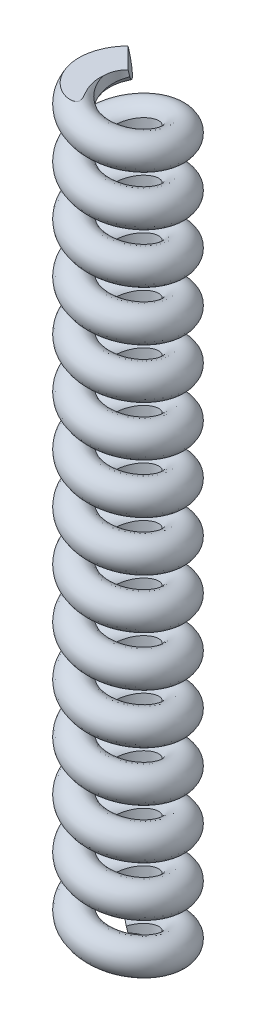
SolidWorks part; units mm, degrees
ref_plane "Front" through (0, 0, 0) normal (0, 0, 1) x (1, 0, 0)
ref_plane "Top" through (0, 0, 0) normal (0, 1, 0) x (1, 0, 0)
ref_plane "Right" through (0, 0, 0) normal (1, 0, 0) x (0, 0, -1)
sketch "Sketch1" plane through (0, 0, 0) normal (0, 1, 0) x (1, 0, 0)
  circle A0 centre (0, 0) radius 3.175
  point P4 (0, 0)
  dimension "D1" = 6.35
curve "Helix/Spiral1" pitch 4.155 height 62.3249 turns 15
sweep "Sweep1" add path "Helix/Spiral1" circular profile diameter 2.54 parameters "D3"=2.54
sketch "Sketch10" plane through (0, 0, 0) normal (1, 0, 0) x (0, 0, -1)
  line L5 (-10.2566, 86.0926) -> (14.7467, 86.0926)
  line L6 (-10.2566, 86.0926) -> (-10.2566, 62.3249)
  line L7 (-10.2566, 62.3249) -> (14.7467, 62.3249)
  line L8 (14.7467, 86.0926) -> (14.7467, 62.3249)
  line L9 (-7.3012, 0) -> (8.8113, 0)
  line L10 (-7.3012, 0) -> (-7.3012, -4.697)
  line L11 (-7.3012, -4.697) -> (8.8113, -4.697)
  line L12 (8.8113, 0) -> (8.8113, -4.697)
  spline S0 degree 3 poles (2.2451, 0) (2.5371, 0.086) (3.0105, 0.2599) (3.2574, 0.5193) (3.0097, 0.7791) (2.3035, 1.0387) (1.2467, 1.2984) (0, 1.5581) (-1.2467, 1.8178) (-2.3035, 2.0775) (-3.0097, 2.3372) (-3.2577, 2.5969) (-3.0097, 2.8566) (-2.3035, 3.1162) (-0.8944, 3.4625) (0.8944, 3.8087) (2.3035, 4.155) (3.0097, 4.4147) (3.2577, 4.6744) (3.0097, 4.9341) (2.3035, 5.1937) (0.8944, 5.54) (-0.8944, 5.8862) (-2.3035, 6.2325) (-3.0097, 6.4922) (-3.2577, 6.7519) (-3.0097, 7.0115) (-2.3035, 7.2712) (-0.8944, 7.6175) (0.8944, 7.9637) (2.3035, 8.31) (3.0097, 8.5697) (3.2577, 8.8294) (3.0097, 9.089) (2.3035, 9.3487) (0.8944, 9.695) (-0.8944, 10.0412) (-2.3035, 10.3875) (-3.0097, 10.6472) (-3.2577, 10.9069) (-3.0097, 11.1665) (-2.3035, 11.4262) (-0.8944, 11.7725) (0.8944, 12.1187) (2.3035, 12.465) (3.0097, 12.7247) (3.2577, 12.9843) (3.0097, 13.244) (2.3035, 13.5037) (0.8944, 13.85) (-0.8944, 14.1962) (-2.3035, 14.5425) (-3.0097, 14.8022) (-3.2577, 15.0618) (-3.0097, 15.3215) (-2.3035, 15.5812) (-0.8944, 15.9275) (0.8944, 16.2737) (2.3035, 16.62) (3.0097, 16.8797) (3.2577, 17.1393) (3.0097, 17.399) (2.3035, 17.6587) (0.8944, 18.005) (-0.8944, 18.3512) (-2.3035, 18.6975) (-3.0097, 18.9572) (-3.2577, 19.2168) (-3.0097, 19.4765) (-2.3035, 19.7362) (-0.8944, 20.0825) (0.8944, 20.4287) (2.3035, 20.775) (3.0097, 21.0346) (3.2577, 21.2943) (3.0097, 21.554) (2.3035, 21.8137) (0.8944, 22.16) (-0.8944, 22.5062) (-2.3035, 22.8525) (-3.0097, 23.1121) (-3.2577, 23.3718) (-3.0097, 23.6315) (-2.3035, 23.8912) (-0.8944, 24.2375) (0.8944, 24.5837) (2.3035, 24.93) (3.0097, 25.1896) (3.2577, 25.4493) (3.0097, 25.709) (2.3035, 25.9687) (0.8944, 26.3149) (-0.8944, 26.6612) (-2.3035, 27.0074) (-3.0097, 27.2671) (-3.2577, 27.5268) (-3.0097, 27.7865) (-2.3035, 28.0462) (-0.8944, 28.3924) (0.8944, 28.7387) (2.3035, 29.0849) (3.0097, 29.3446) (3.2577, 29.6043) (3.0097, 29.864) (2.3035, 30.1237) (0.8944, 30.4699) (-0.8944, 30.8162) (-2.3035, 31.1624) (-3.0097, 31.4221) (-3.2577, 31.6818) (-3.0097, 31.9415) (-2.3035, 32.2012) (-0.8944, 32.5474) (0.8944, 32.8937) (2.3035, 33.2399) (3.0097, 33.4996) (3.2577, 33.7593) (3.0097, 34.019) (2.3035, 34.2787) (0.8944, 34.6249) (-0.8944, 34.9712) (-2.3035, 35.3174) (-3.0097, 35.5771) (-3.2577, 35.8368) (-3.0097, 36.0965) (-2.3035, 36.3562) (-0.8944, 36.7024) (0.8944, 37.0487) (2.3035, 37.3949) (3.0097, 37.6546) (3.2577, 37.9143) (3.0097, 38.174) (2.3035, 38.4337) (0.8944, 38.7799) (-0.8944, 39.1262) (-2.3035, 39.4724) (-3.0097, 39.7321) (-3.2577, 39.9918) (-3.0097, 40.2515) (-2.3035, 40.5112) (-0.8944, 40.8574) (0.8944, 41.2037) (2.3035, 41.5499) (3.0097, 41.8096) (3.2577, 42.0693) (3.0097, 42.329) (2.3035, 42.5887) (0.8944, 42.9349) (-0.8944, 43.2812) (-2.3035, 43.6274) (-3.0097, 43.8871) (-3.2577, 44.1468) (-3.0097, 44.4065) (-2.3035, 44.6662) (-0.8944, 45.0124) (0.8944, 45.3587) (2.3035, 45.7049) (3.0097, 45.9646) (3.2577, 46.2243) (3.0097, 46.484) (2.3035, 46.7437) (0.8944, 47.0899) (-0.8944, 47.4362) (-2.3035, 47.7824) (-3.0097, 48.0421) (-3.2577, 48.3018) (-3.0097, 48.5615) (-2.3035, 48.8212) (-0.8944, 49.1674) (0.8944, 49.5137) (2.3035, 49.8599) (3.0097, 50.1196) (3.2577, 50.3793) (3.0097, 50.639) (2.3035, 50.8987) (0.8944, 51.2449) (-0.8944, 51.5912) (-2.3035, 51.9374) (-3.0097, 52.1971) (-3.2577, 52.4568) (-3.0097, 52.7165) (-2.3035, 52.9761) (-0.8944, 53.3224) (0.8944, 53.6686) (2.3035, 54.0149) (3.0097, 54.2746) (3.2577, 54.5343) (3.0097, 54.794) (2.3035, 55.0536) (0.8944, 55.3999) (-0.8944, 55.7461) (-2.3035, 56.0924) (-3.0097, 56.3521) (-3.2577, 56.6118) (-3.0097, 56.8715) (-2.3035, 57.1311) (-0.8944, 57.4774) (0.8944, 57.8236) (2.3035, 58.1699) (3.0097, 58.4296) (3.2577, 58.6893) (3.0097, 58.9489) (2.3035, 59.2086) (0.8944, 59.5549) (-0.8944, 59.9011) (-2.3035, 60.2474) (-3.0097, 60.5071) (-3.2577, 60.7668) (-3.0097, 61.0264) (-2.3035, 61.2861) (-1.2467, 61.5458) (0.0002, 61.8056) (1.2458, 62.0649) (1.953, 62.2388) (2.2451, 62.3249) knots 0 0 0 0 0.004167 0.008333 0.0125 0.016667 0.020833 0.025 0.029167 0.033333 0.0375 0.041667 0.045833 0.05 0.054167 0.0625 0.066667 0.070833 0.075 0.079167 0.083333 0.0875 0.095833 0.1 0.104167 0.108333 0.1125 0.116667 0.120833 0.129167 0.133333 0.1375 0.141667 0.145833 0.15 0.154167 0.1625 0.166667 0.170833 0.175 0.179167 0.183333 0.1875 0.195833 0.2 0.204167 0.208333 0.2125 0.216667 0.220833 0.229167 0.233333 0.2375 0.241667 0.245833 0.25 0.254167 0.2625 0.266667 0.270833 0.275 0.279167 0.283333 0.2875 0.295833 0.3 0.304167 0.308333 0.3125 0.316667 0.320833 0.329167 0.333333 0.3375 0.341667 0.345833 0.35 0.354167 0.3625 0.366667 0.370833 0.375 0.379167 0.383333 0.3875 0.395833 0.4 0.404167 0.408333 0.4125 0.416667 0.420833 0.429167 0.433333 0.4375 0.441667 0.445833 0.45 0.454167 0.4625 0.466667 0.470833 0.475 0.479167 0.483333 0.4875 0.495833 0.5 0.504167 0.508333 0.5125 0.516667 0.520833 0.529167 0.533333 0.5375 0.541667 0.545833 0.55 0.554167 0.5625 0.566667 0.570833 0.575 0.579167 0.583333 0.5875 0.595833 0.6 0.604167 0.608333 0.6125 0.616667 0.620833 0.629167 0.633333 0.6375 0.641667 0.645833 0.65 0.654167 0.6625 0.666667 0.670833 0.675 0.679167 0.683333 0.6875 0.695833 0.7 0.704167 0.708333 0.7125 0.716667 0.720833 0.729167 0.733333 0.7375 0.741667 0.745833 0.75 0.754167 0.7625 0.766667 0.770833 0.775 0.779167 0.783333 0.7875 0.795833 0.8 0.804167 0.808333 0.8125 0.816667 0.820833 0.829167 0.833333 0.8375 0.841667 0.845833 0.85 0.854167 0.8625 0.866667 0.870833 0.875 0.879167 0.883333 0.8875 0.895833 0.9 0.904167 0.908333 0.9125 0.916667 0.920833 0.929167 0.933333 0.9375 0.941667 0.945833 0.95 0.954167 0.9625 0.966667 0.970833 0.975 0.979167 0.983333 0.9875 0.991667 0.995833 1 1 1 1 construction
  point P8 (2.2451, 62.3249)
  point P9 (2.2451, 0)
  point P12 (2.2451, 62.3249)
extrude "TopandBottom" cut sketch "Sketch10" against normal through all both and the other way through all
sketch "Sketch13" plane through (0, 0, 0) normal (0, 1, 0) x (1, 0, 0)
  circle A0 centre (0, 0) radius 2.019
extrude "CentralHole" cut sketch "Sketch13" against normal through all both and the other way through all
